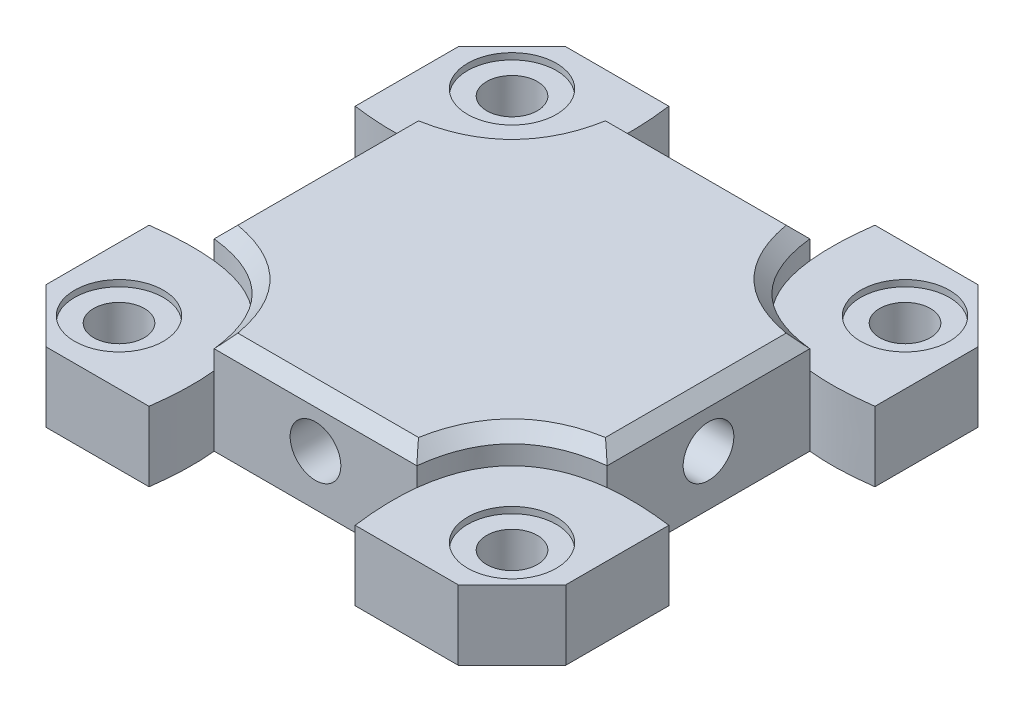
SolidWorks part; units mm, degrees
ref_plane "Front Plane" through (0, 0, 0) normal (0, 0, 1) x (1, 0, 0)
ref_plane "Top Plane" through (0, 0, 0) normal (0, 1, 0) x (1, 0, 0)
ref_plane "Right Plane" through (0, 0, 0) normal (1, 0, 0) x (0, 0, -1)
sketch "Sketch2" plane through (0, 0, 0) normal (0, 1, 0) x (1, 0, 0)
  line L1 (-20.5, -20.5) -> (20.5, -20.5)
  line L2 (-20.5, -20.5) -> (-20.5, 20.5)
  line L3 (-20.5, 20.5) -> (20.5, 20.5)
  line L4 (20.5, -20.5) -> (20.5, 20.5)
  line L5 (-20.5, -20.5) -> (20.5, 20.5) construction
  line L6 (-20.5, 20.5) -> (20.5, -20.5) construction
  point P0 (0, 0)
  dimension "D1" = 41
  dimension "D2" = 41
extrude "Boss-Extrude1" add sketch "Sketch2" along normal blind 2
sketch "Sketch3" plane through (0, 0, 0) normal (0, -1, 0) x (1, 0, 0)
  line L0 (-7.9432, -8.0372) -> (0, 0) construction
  line L5 (-7.9432, -8.0372) -> (7.9432, -8.0372) construction
  line L6 (-7.9432, -8.0372) -> (-7.9432, 8.0372) construction
  line L7 (-7.9432, 8.0372) -> (7.9432, 8.0372) construction
  line L8 (7.9432, -8.0372) -> (7.9432, 8.0372) construction
  line L9 (0, 0) -> (7.9432, 8.0372) construction
  line L10 (0, 0) -> (7.9432, -8.0372) construction
  line L11 (-7.9432, 8.0372) -> (0, 0) construction
  arc A1 (7.9432, 8.0372) -> (-7.9432, 8.0372) centre (0, 0) ccw construction
  arc A2 (-7.9432, -8.0372) -> (7.9432, -8.0372) centre (0, 0) ccw construction
  arc A3 (-7.9432, 8.0372) -> (-7.9432, -8.0372) centre (0, 0) ccw construction
  arc A4 (7.9432, -8.0372) -> (8.0686, 7.9112) centre (0, 0) ccw construction
  circle A5 centre (-7.9432, 8.0372) radius 2
  circle A10 centre (8.0372, 7.9432) radius 2
  circle A12 centre (7.9432, -8.0372) radius 2
  circle A13 centre (-8.0372, -7.9432) radius 2
  arc A14 (8.0686, 7.9112) -> (7.9432, 8.0372) centre (0, 0) ccw construction
  point P15 (-1.4144, -0.0142)
  point P19 (0, 0)
  dimension "D1" = 22.6
  dimension "D2" = 4
  dimension "D4" = 4
extrude "Cut-Extrude1" cut sketch "Sketch3" against normal through all
sketch "Sketch4" plane through (0, 2, 0) normal (0, 1, 0) x (1, 0, 0)
  circle A0 centre (0, 0) radius 7.5
  dimension "D1" = 15
extrude "Cut-Extrude2" cut sketch "Sketch4" against normal through all
sketch "Sketch5" plane through (0, 0, 0) normal (0, -1, 0) x (1, 0, 0)
  line L1 (-12.5, -12.5) -> (12.5, -12.5)
  line L2 (-12.5, -12.5) -> (-12.5, 12.5)
  line L3 (-12.5, 12.5) -> (12.5, 12.5)
  line L4 (12.5, -12.5) -> (12.5, 12.5)
  line L5 (-12.5, -12.5) -> (12.5, 12.5) construction
  line L6 (-12.5, 12.5) -> (12.5, -12.5) construction
  point P0 (0, 0)
  dimension "D1" = 25
  dimension "D2" = 25
extrude "Cut-Extrude3" cut sketch "Sketch5" against normal blind 1
sketch "Sketch6" plane through (0, 2, 0) normal (0, 1, 0) x (1, 0, 0)
  line L0 (-20.5, 16.2574) -> (-16.2574, 20.5)
  line L1 (-20.5, 20.5) -> (-20.5, -20.5) construction
  line L2 (20.5, 20.5) -> (-20.5, 20.5) construction
  line L4 (16.2574, 20.5) -> (20.5, 16.2574)
  line L5 (20.5, -20.5) -> (20.5, 20.5) construction
  line L7 (20.5, -16.2574) -> (16.2574, -20.5)
  line L8 (-20.5, -20.5) -> (20.5, -20.5) construction
  line L10 (-16.2574, -20.5) -> (-20.5, -16.2574)
  line L12 (-2.4898, 0) -> (5.6129, 0) construction
  line L13 (0, 5.0948) -> (0, 0) construction
  line L14 (0, 0) -> (3.8649, 3.8649) construction
  line L15 (-20.5, -16.2574) -> (-20.5, -20.5)
  line L16 (-20.5, -20.5) -> (-16.2574, -20.5)
  line L17 (16.2574, -20.5) -> (20.5, -20.5)
  line L18 (20.5, -20.5) -> (20.5, -16.2574)
  line L19 (20.5, 16.2574) -> (20.5, 20.5)
  line L20 (20.5, 20.5) -> (16.2574, 20.5)
  line L21 (-16.2574, 20.5) -> (-20.5, 20.5)
  line L22 (-20.5, 20.5) -> (-20.5, 16.2574)
  dimension "D1" = 6
  dimension "D2" = 6
  dimension "D3" = 45
  dimension "D4" = 6
  dimension "D5" = 6
extrude "Cut-Extrude4" cut sketch "Sketch6" against normal through all
sketch "Sketch7" plane through (0, 0, 0) normal (0, -1, 0) x (1, 0, 0)
  line L0 (-15.5, 15.5) -> (0, 0) construction
  line L1 (-15.5, -15.5) -> (15.5, -15.5) construction
  line L2 (-15.5, -15.5) -> (-15.5, 15.5) construction
  line L3 (-15.5, 15.5) -> (15.5, 15.5) construction
  line L4 (15.5, -15.5) -> (15.5, 15.5) construction
  line L5 (-15.5, -15.5) -> (0, 0) construction
  line L6 (0, 0) -> (15.5, -15.5) construction
  line L7 (0, 0) -> (15.5, 15.5) construction
  arc A0 (-15.5, -15.5) -> (15.5, -15.5) centre (0, 0) ccw construction
  arc A1 (-15.5, 15.5) -> (-15.5, -15.5) centre (0, 0) ccw construction
  arc A2 (15.5, -15.5) -> (15.5, 15.5) centre (0, 0) ccw construction
  arc A3 (15.5, 15.5) -> (-15.5, 15.5) centre (0, 0) ccw construction
  circle A4 centre (-15.5, 15.5) radius 2
  circle A5 centre (15.5, 15.5) radius 2
  circle A6 centre (15.5, -15.5) radius 2
  circle A7 centre (-15.5, -15.5) radius 2
  point P16 (0, 0)
  dimension "D2" = 4
  dimension "D4" = 31
  dimension "D3" = 4
extrude "Cut-Extrude5" cut sketch "Sketch7" against normal through all
sketch "Sketch8" plane through (0, 0, 0) normal (0, -1, 0) x (1, 0, 0)
  line L0 (-12.5, -12.5) -> (-12.5, 12.5) construction
  line L1 (-12.5, -12.5) -> (-20.477, -12.5) construction
  line L2 (-12.5, 12.5) -> (-20.477, 12.5) construction
  line L3 (-20.477, -12.5) -> (-20.477, 12.5) construction
  line L4 (12.5, -12.5) -> (12.5, 12.5) construction
  line L5 (12.5, -12.5) -> (20.4876, -12.5) construction
  line L6 (12.5, 12.5) -> (20.4876, 12.5) construction
  line L7 (20.4876, -12.5) -> (20.4876, 12.5) construction
  line L8 (-12.5, 12.5) -> (12.5, 12.5)
  line L9 (-12.5, 12.5) -> (-12.5, 20.5)
  line L10 (12.5, 12.5) -> (12.5, 20.5)
  line L11 (-12.5, 20.5) -> (12.5, 20.5)
  line L12 (12.5, -12.5) -> (-12.5, -12.5)
  line L13 (12.5, -12.5) -> (12.5, -20.4578)
  line L14 (-12.5, -12.5) -> (-12.5, -20.4578)
  line L15 (12.5, -20.4578) -> (-12.5, -20.4578)
  line L16 (-16.2574, 20.5) -> (16.2574, 20.5) construction
extrude "Boss-Extrude2" add sketch "Sketch8" along normal blind 3.5
sketch "Sketch9" plane through (0, -3.5, 0) normal (0, -1, 0) x (1, 0, 0)
  circle A0 centre (0, 16.5) radius 2
  circle A1 centre (0, -16.4789) radius 2
  dimension "D1" = 4
extrude "Cut-Extrude6" cut sketch "Sketch9" against normal through all
sketch "Sketch10" plane through (0, 0, 0) normal (0, -1, 0) x (1, 0, 0)
  line L0 (-20.5, -16.2574) -> (-16.2574, -20.5)
  line L1 (20.5, 12.5) -> (12.5, 12.5)
  line L2 (20.5, 12.5) -> (20.5, 16.2574)
  line L3 (16.2574, 20.5) -> (12.5, 20.5)
  line L4 (-20.5, 12.5) -> (-20.5, 16.2574)
  line L5 (-20.5, -12.5) -> (-12.5, -12.5)
  line L6 (-20.5, -12.5) -> (-20.5, -16.2574)
  line L8 (20.5, -12.5) -> (20.5, -16.2574)
  line L9 (-20.5, 16.2574) -> (-16.2574, 20.5)
  line L10 (16.2574, 20.5) -> (20.5, 16.2574)
  line L11 (20.5, -16.2574) -> (16.2574, -20.5)
  line L12 (-20.5, -12.5) -> (-20.5, -16.2574)
  line L13 (-12.5, 12.5) -> (-20.5, 12.5)
  line L14 (-12.5, 20.5) -> (-16.2574, 20.5)
  line L15 (12.5, -12.5) -> (20.5, -12.5)
  line L16 (-12.5, -12.5) -> (-12.5, 12.5)
  line L17 (-12.5, 12.5) -> (-12.5, 20.5)
  line L18 (-12.5, 20.5) -> (-16.2574, 20.5)
  line L19 (-16.2574, 20.5) -> (-20.5, 16.2574)
  line L20 (-20.5, 16.2574) -> (-20.5, -16.2574)
  line L21 (-20.5, -16.2574) -> (-16.2574, -20.5)
  line L22 (-16.2574, -20.5) -> (16.2574, -20.5)
  line L23 (16.2574, -20.5) -> (20.5, -16.2574)
  line L24 (20.5, -16.2574) -> (20.5, 16.2574)
  line L25 (20.5, 16.2574) -> (16.2574, 20.5)
  line L26 (16.2574, 20.5) -> (12.5, 20.5)
  line L27 (12.5, 20.5) -> (12.5, 12.5)
  line L28 (12.5, 12.5) -> (12.5, -12.5)
  line L29 (12.5, -12.5) -> (12.5, -20.4578)
  line L30 (12.5, -20.4578) -> (-12.5, -20.4578)
  line L31 (-12.5, -20.4578) -> (-12.5, -12.5)
  line L33 (-12.5, 12.5) -> (-12.5, 20.5)
  line L34 (-12.5, 20.5) -> (-16.2574, 20.5)
  line L35 (-16.2574, 20.5) -> (-20.5, 16.2574)
  line L36 (-20.5, 16.2574) -> (-20.5, 12.5)
  line L37 (-20.5, -16.2574) -> (-16.2574, -20.5)
  line L39 (16.2574, -20.5) -> (20.5, -16.2574)
  line L40 (20.5, -16.2574) -> (20.5, 16.2574)
  line L41 (20.5, 16.2574) -> (16.2574, 20.5)
  line L42 (16.2574, 20.5) -> (12.5, 20.5)
  line L43 (12.5, 20.5) -> (12.5, 12.5)
  line L44 (12.5, 12.5) -> (12.5, -12.5)
  line L45 (12.5, -12.5) -> (12.5, -20.4578)
  line L47 (-12.5, -20.4578) -> (-12.5, -12.5)
  line L50 (12.5, 20.5) -> (-12.5, 20.5) construction
  circle A0 centre (-15.5, 15.5) radius 2
  circle A1 centre (15.5, 15.5) radius 2
  circle A2 centre (15.5, -15.5) radius 2
  circle A3 centre (-15.5, -15.5) radius 2
  circle M19 centre (-15.5, -15.5) radius 2
  circle M20 centre (15.5, -15.5) radius 2
  circle M21 centre (15.5, 15.5) radius 2
  circle M22 centre (-15.5, 15.5) radius 2
  line M24 (-12.5, 12.5) -> (-12.5, 20.5)
  line M25 (-12.5, 20.5) -> (-16.2574, 20.5)
  line M26 (-16.2574, 20.5) -> (-20.5, 16.2574)
  line M27 (-20.5, 16.2574) -> (-20.5, -16.2574)
  line M28 (-20.5, -16.2574) -> (-16.2574, -20.5)
  line M29 (-16.2574, -20.5) -> (16.2574, -20.5)
  line M30 (16.2574, -20.5) -> (20.5, -16.2574)
  line M31 (20.5, -16.2574) -> (20.5, 16.2574)
  line M32 (20.5, 16.2574) -> (16.2574, 20.5)
  line M33 (16.2574, 20.5) -> (12.5, 20.5)
  line M34 (12.5, 20.5) -> (12.5, 12.5)
  line M36 (12.5, -12.5) -> (12.5, -20.4578)
  line M37 (12.5, -20.4578) -> (-12.5, -20.4578)
  line M38 (-12.5, -20.4578) -> (-12.5, -12.5)
  dimension "D1" = 0
extrude "Boss-Extrude3" add sketch "Sketch10" along normal up to surface (3.5 mm away) contours L13 M24 M25 M26 M27 M22 | L1 M31 M32 M33 M34 M21 | L15 L5 M36 M37 M38 M27 M28 M29 M30 M31 M19 M20 up to face at (0, -3.5, 14.5)
sketch "Sketch11" plane through (0, 2, 0) normal (0, 1, 0) x (1, 0, 0)
  circle A0 centre (-15.5, 15.5) radius 3.5
  circle A1 centre (15.5, 15.5) radius 3.5
  circle A2 centre (15.5, -15.5) radius 3.5
  circle A3 centre (-15.5, -15.5) radius 3.5
  point P12 (0, 0)
  dimension "D1" = 7
  dimension "D2" = 4
extrude "Cut-Extrude7" cut sketch "Sketch11" against normal offset from surface (3.5 mm away) 2 up to face at (0, -3.5, -18.4789)
sketch "Sketch12" plane through (0, 0, 0) normal (0, -1, 0) x (1, 0, 0)
  line L0 (-12.5, 12.5) -> (-12.5, -12.5) construction
  line L1 (-20.5, -12.5) -> (-12.5, -12.5)
  line L2 (-20.5, -12.5) -> (-20.5, -10.5)
  line L3 (-20.5, -10.5) -> (-12.5, -10.5)
  line L4 (-12.5, -12.5) -> (-12.5, -10.5)
  line L5 (-25.9518, 0) -> (26.3784, 0) construction
  line L6 (0, 23.4974) -> (0, -23.7021) construction
  line L7 (-12.5, 12.5) -> (-12.5, 10.5)
  line L8 (-20.5, 12.5) -> (-12.5, 12.5)
  line L9 (-20.5, 12.5) -> (-20.5, 10.5)
  line L10 (-20.5, 10.5) -> (-12.5, 10.5)
  line L11 (12.5, -12.5) -> (12.5, -10.5)
  line L12 (20.5, -10.5) -> (12.5, -10.5)
  line L13 (20.5, -12.5) -> (20.5, -10.5)
  line L14 (20.5, -12.5) -> (12.5, -12.5)
  line L15 (20.5, 10.5) -> (12.5, 10.5)
  line L16 (20.5, 12.5) -> (20.5, 10.5)
  line L17 (20.5, 12.5) -> (12.5, 12.5)
  line L18 (12.5, 12.5) -> (12.5, 10.5)
  dimension "D1" = 2
extrude "Boss-Extrude4" add sketch "Sketch12" along normal up to surface (3.5 mm away) up to face at (0, -3.5, 14.5)
sketch "Sketch13" plane through (0, 2, 0) normal (0, 1, 0) x (1, 0, 0)
  circle A0 centre (-15.5, 15.5) radius 3.5
  circle A1 centre (15.5, 15.5) radius 3.5
  circle A2 centre (15.5, -15.5) radius 3.5
  circle A3 centre (-15.5, -15.5) radius 3.5
  point P12 (0, 0)
  dimension "D1" = 4
extrude "Cut-Extrude8" cut sketch "Sketch13" against normal up to surface (3.5 mm away) up to face at (-15.5, -1.5, -13.5)
sketch "Sketch14" plane through (0, -1.5, 0) normal (0, 1, 0) x (1, 0, 0)
  circle A0 centre (-15.5, -15.5) radius 2
  circle A1 centre (-15.5, -15.5) radius 3.5
  circle A2 centre (-15.5, 15.5) radius 3.5
  circle A3 centre (-15.5, 15.5) radius 2
  circle A4 centre (15.5, 15.5) radius 3.5
  circle A5 centre (15.5, 15.5) radius 2
  circle A6 centre (15.5, -15.5) radius 3.5
  circle A7 centre (15.5, -15.5) radius 2
  point P16 (0, 0)
  dimension "D1" = 4
extrude "Boss-Extrude5" add sketch "Sketch14" along normal offset from surface (3 mm away) 0.5 up to face at (-15.5, 2, 19)
sketch "Sketch15" plane through (0, 2, 0) normal (0, 1, 0) x (1, 0, 0)
  line L0 (0, 20.5) -> (0, -20.5) construction
  line L1 (16.2574, 20.5) -> (-16.2574, 20.5) construction
  line L2 (-16.2574, -20.5) -> (16.2574, -20.5) construction
  line L3 (0, -16.5) -> (8, -16.5) construction
  line L4 (0, -16.5) -> (-8, -16.5) construction
  line L5 (0, 16.4789) -> (8, 16.4789) construction
  line L6 (0, 16.4789) -> (-8, 16.4789) construction
  line L7 (-8, 20.5) -> (-8, 16.4789) construction
  line L8 (-8, 16.4789) -> (-8, 12.4578) construction
  line L9 (-8, -20.5) -> (-8, -16.5) construction
  line L10 (-8, -16.5) -> (-8, -12.5) construction
  line L11 (-3.025, 0) -> (3.025, 0) construction
  line L12 (8, 12.4578) -> (-8, 12.4578)
  line L13 (8, 12.4578) -> (8, 20.5)
  line L14 (8, 20.5) -> (-8, 20.5)
  line L15 (-8, 12.4578) -> (-8, 20.5)
  line L16 (8, -12.5) -> (-8, -12.5)
  line L17 (8, -12.5) -> (8, -20.5)
  line L18 (8, -20.5) -> (-8, -20.5)
  line L19 (-8, -12.5) -> (-8, -20.5)
  circle A0 centre (0, 16.4789) radius 2
  circle A1 centre (0, -16.4789) radius 2
  dimension "D1" = 8
extrude "Boss-Extrude6" add sketch "Sketch15" along normal blind 4
chamfer "Chamfer1" distance 0.5 angle 45 2 edges at (0, 6, 14.4789) (0, 6, -14.4789)
chamfer "Chamfer2" distance 0.5 angle 45 8 edges at (8, 6, 16.5) (0, 6, 20.5) (-8, 6, 16.5) (0, 6, 12.5) (-8, 6, -16.4789) (0, 6, -20.5) (8, 6, -16.4789) (0, 6, -12.4578)
sketch "Sketch16" plane through (0, -3.5, 0) normal (0, -1, 0) x (1, 0, 0)
  line L0 (-20.5, 10.5) -> (-20.5, 16.2574) construction
  line L1 (-12.5, -12.5) -> (-20.5, -12.5)
  line L2 (-12.5, -12.5) -> (-12.5, 12.5)
  line L3 (-12.5, 12.5) -> (-20.5, 12.5)
  line L4 (-20.5, -12.5) -> (-20.5, 12.5)
  line L5 (12.5, 12.5) -> (20.5, 12.5)
  line L6 (12.5, 12.5) -> (12.5, -12.5)
  line L7 (20.5, 12.5) -> (20.5, -12.5)
  line L8 (12.5, -12.5) -> (20.5, -12.5)
  line L9 (20.5, 16.2574) -> (20.5, 10.5) construction
extrude "Cut-Extrude9" cut sketch "Sketch16" against normal up to surface (3.5 mm away) up to face at (16.5, 0, 0)
sketch "Sketch17" plane through (0, 6, 0) normal (0, 1, 0) x (1, 0, 0)
  line L1 (15.3001, -24.9451) -> (-15.3001, -24.9451)
  line L2 (15.3001, -24.9451) -> (15.3001, 24.9451)
  line L3 (15.3001, 24.9451) -> (-15.3001, 24.9451)
  line L4 (-15.3001, -24.9451) -> (-15.3001, 24.9451)
  line L5 (15.3001, -24.9451) -> (-15.3001, 24.9451) construction
  line L6 (15.3001, 24.9451) -> (-15.3001, -24.9451) construction
  point P0 (0, 0)
extrude "Cut-Extrude10" cut sketch "Sketch17" against normal up to surface (4 mm away) up to face at (0, 2, 0.0053)
sketch "Sketch18" plane through (0, 2, 0) normal (0, 1, 0) x (1, 0, 0)
  circle A0 centre (0, 0) radius 14.015
extrude "Boss-Extrude7" add sketch "Sketch18" against normal up to surface (1 mm away) up to face at (8.0372, 1, 9.9432)
sketch "Sketch19" plane through (0, 2, 0) normal (0, 1, 0) x (1, 0, 0)
  circle A0 centre (0, 16.4789) radius 2
  circle A1 centre (0, -16.5) radius 2
extrude "Boss-Extrude8" add sketch "Sketch19" against normal up to surface (5.5 mm away) up to face at (0, -3.5, -18.4789)
sketch "Sketch20" plane through (0, 2, 0) normal (0, 1, 0) x (1, 0, 0)
  line L0 (0, 0) -> (-10, 0) construction
  circle A0 centre (-10, 0) radius 2
  circle A1 centre (0, 10) radius 2
  circle A2 centre (10, 0) radius 2
  circle A3 centre (0, -10) radius 2
  point P13 (0, 0)
  dimension "D2" = 4
  dimension "D1" = 10
  dimension "D3" = 4
sketch "Sketch21" plane through (0, 1, 0) normal (0, -1, 0) x (1, 0, 0)
  line L0 (-20.5, -16.2574) -> (-20.5, -12.5) construction
  line L1 (20.5, 12.5) -> (-20.5, 12.5)
  line L2 (20.5, 12.5) -> (20.5, -12.5)
  line L3 (20.5, -12.5) -> (-20.5, -12.5)
  line L4 (-20.5, 12.5) -> (-20.5, -12.5)
  line L5 (20.5, 12.5) -> (-20.5, -12.5) construction
  line L6 (20.5, -12.5) -> (-20.5, 12.5) construction
  line L7 (20.5, -12.5) -> (-20.5, -12.5) construction
  point P0 (0, 0)
extrude "Boss-Extrude9" add sketch "Sketch21" along normal up to surface (4.5 mm away) up to face at (0, -3.5, -16.4191)
sketch "Sketch22" plane through (0, 2, 0) normal (0, 1, 0) x (1, 0, 0)
  line L0 (0, 20.5) -> (0, 0) construction
  line L1 (16.2574, 20.5) -> (-16.2574, 20.5) construction
  line L2 (0, 0) -> (-20.5, 0) construction
  line L3 (-20.5, 16.2574) -> (-20.5, -16.2574) construction
  line L4 (0, 0) -> (0, -20.5) construction
  line L5 (-16.2574, -20.5) -> (16.2574, -20.5) construction
  line L6 (0, 0) -> (20.5, 0) construction
  line L7 (20.5, -16.2574) -> (20.5, 16.2574) construction
  line L8 (-20.5, 0) -> (-20.5, 16.2574) construction
  line L9 (0, 20.5) -> (-16.2574, 20.5) construction
  line L10 (-20.5, 0) -> (-20.5, -16.2574) construction
  line L11 (0, -20.5) -> (-16.2574, -20.5) construction
  line L12 (-8.1287, -20.5) -> (-20.5, -8.1287) construction
  line L13 (-8.1287, 20.5) -> (-20.5, 8.1287) construction
  line L14 (0, -20.5) -> (16.2574, -20.5) construction
  line L15 (20.5, 0) -> (20.5, -16.2574) construction
  line L16 (8.1287, -20.5) -> (20.5, -8.1287) construction
  line L17 (0, 20.5) -> (16.2574, 20.5) construction
  line L18 (20.5, 16.2574) -> (20.5, 0) construction
  line L19 (20.5, 8.1287) -> (8.1287, 20.5) construction
  line L20 (-14.3143, 14.3143) -> (-10.25, 10.25) construction
  line L21 (-10.25, -10.25) -> (-14.3143, -14.3143) construction
  line L22 (-20.5, 0) -> (0, 20.5) construction
  line L23 (0, 20.5) -> (20.5, 0) construction
  line L24 (20.5, 0) -> (0, -20.5) construction
  line L25 (0, -20.5) -> (-20.5, 0) construction
  line L26 (10.25, 10.25) -> (14.3143, 14.3143) construction
  line L27 (10.25, -10.25) -> (14.3143, -14.3143) construction
  line L28 (-20.5, 8.1287) -> (-20.5, -8.1287)
  line L29 (-8.1287, -20.5) -> (8.1287, -20.5)
  line L30 (20.5, -8.1287) -> (20.5, 8.1287)
  line L31 (-8.1287, 20.5) -> (8.1287, 20.5)
  spline S0 degree 2 poles (-8.1287, 20.5) (-6.1857, 6.1857) (-20.5, 8.1287) knots 0 0 0 1 1 1
  spline S1 degree 2 poles (8.1287, -20.5) (6.1857, -6.1857) (20.5, -8.1287) knots 0 0 0 1 1 1
  spline S2 degree 2 poles (-20.5, -8.1287) (-6.1857, -6.1857) (-8.1287, -20.5) knots 0 0 0 1 1 1
  spline S3 degree 2 poles (8.1287, 20.5) (6.1857, 6.1857) (20.5, 8.1287) knots 0 0 0 1 1 1
extrude "Boss-Extrude10" add sketch "Sketch22" along normal blind 2.5
sketch "Sketch24" plane through (0, 4.5, 0) normal (0, 1, 0) x (1, 0, 0)
  line L0 (-7.9931, 15.5) -> (7.9931, 15.5) construction
  line L1 (15.5, 7.9931) -> (15.5, -7.9931) construction
  line L2 (7.9931, -15.5) -> (-7.9931, -15.5) construction
  line L3 (-15.5, -7.9931) -> (-15.5, 7.9931) construction
  line L4 (-20.5, 8.1287) -> (-20.5, -8.1287)
  line L5 (-8.1287, -20.5) -> (8.1287, -20.5)
  line L6 (20.5, -8.1287) -> (20.5, 8.1287)
  line L7 (8.1287, 20.5) -> (-8.1287, 20.5)
  line L8 (-20.5, 8.1287) -> (-20.5, -8.1287)
  line L9 (-8.1287, -20.5) -> (8.1287, -20.5)
  line L10 (20.5, -8.1287) -> (20.5, 8.1287)
  line L11 (8.1287, 20.5) -> (-8.1287, 20.5)
  line L12 (-7.9931, 15.5) -> (7.9931, 15.5)
  line L13 (15.5, 7.9931) -> (15.5, -7.9931)
  line L14 (7.9931, -15.5) -> (-7.9931, -15.5)
  line L15 (-15.5, -7.9931) -> (-15.5, 7.9931)
  parabola Q0 (-7.9931, -15.5) -> (-8.1287, -20.5) focus (-12.6035, -12.6035) apex (-10.25, -10.25)
  parabola Q1 (-15.5, 7.9931) -> (-20.5, 8.1287) focus (-12.6035, 12.6035) apex (-10.25, 10.25)
  parabola Q2 (7.9931, 15.5) -> (8.1287, 20.5) focus (12.6035, 12.6035) apex (10.25, 10.25)
  parabola Q3 (15.5, -7.9931) -> (20.5, -8.1287) focus (12.6035, -12.6035) apex (10.25, -10.25)
  parabola Q4 (-8.1287, 20.5) -> (-20.5, 8.1287) focus (-12.6035, 12.6035) apex (-10.25, 10.25)
  parabola Q5 (-20.5, -8.1287) -> (-8.1287, -20.5) focus (-12.6035, -12.6035) apex (-10.25, -10.25)
  parabola Q6 (8.1287, -20.5) -> (20.5, -8.1287) focus (12.6035, -12.6035) apex (10.25, -10.25)
  parabola Q7 (20.5, 8.1287) -> (8.1287, 20.5) focus (12.6035, 12.6035) apex (10.25, 10.25)
  parabola Q8 (-8.1287, 20.5) -> (-7.9931, 15.5) focus (-12.6035, 12.6035) apex (-10.25, 10.25)
  parabola Q9 (-20.5, -8.1287) -> (-15.5, -7.9931) focus (-12.6035, -12.6035) apex (-10.25, -10.25)
  parabola Q10 (8.1287, -20.5) -> (7.9931, -15.5) focus (12.6035, -12.6035) apex (10.25, -10.25)
  parabola Q11 (20.5, 8.1287) -> (15.5, 7.9931) focus (12.6035, 12.6035) apex (10.25, 10.25)
  dimension "D1" = 0
extrude "Cut-Extrude12" cut sketch "Sketch24" against normal through all
sketch "Sketch25" plane through (0, 0, 15.5) normal (0, 0, 1) x (1, 0, 0)
  line L0 (-7.9931, 4.5) -> (7.9931, -3.5) construction
  line L1 (-7.9931, -3.5) -> (7.9931, 4.5) construction
  line L2 (7.9931, 2) -> (7.9931, 4.5) construction
  circle A0 centre (0, 0.5) radius 2
  dimension "D1" = 4
extrude "Cut-Extrude13" cut sketch "Sketch25" against normal blind 5
mirror "Mirror1" about plane through (0, 0, 0) normal (0, 0, 1) of "Cut-Extrude13"
sketch "Sketch26" plane through (15.5, 0, 0) normal (1, 0, 0) x (0, 0, -1)
  line L0 (7.9931, -3.5) -> (-7.9931, 4.5) construction
  line L1 (-7.9931, -3.5) -> (7.9931, 4.5) construction
  circle A0 centre (0, 0.5) radius 2
  dimension "D1" = 4
extrude "Cut-Extrude14" cut sketch "Sketch26" against normal blind 5
mirror "Mirror2" about plane through (0, 0, 0) normal (1, 0, 0) of "Cut-Extrude14"
chamfer "Chamfer3" distance 1 angle 45 8 edges
